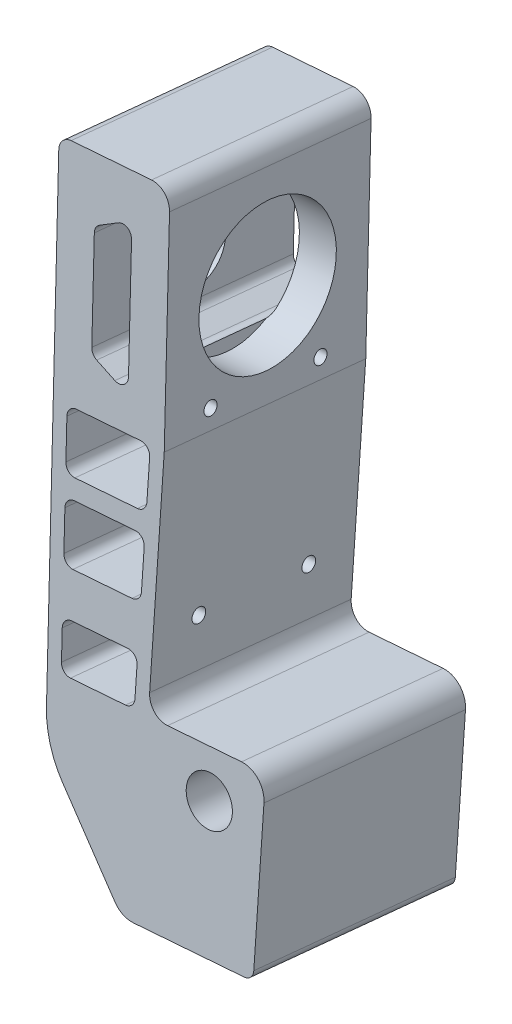
SolidWorks part; units mm, degrees
ref_plane "Front Plane" through (0, 0, 0) normal (0, 0, 1) x (1, 0, 0)
ref_plane "Top Plane" through (0, 0, 0) normal (0, 1, 0) x (1, 0, 0)
ref_plane "Right Plane" through (0, 0, 0) normal (1, 0, 0) x (0, 0, -1)
sketch "Sketch2" plane through (0, 5.1848, 52.754) normal (0, 0.0978, 0.9952) x (1, 0, 0)
  line L0 (-79.3386, 60.0196) -> (-86.1713, 157.1826)
  line L1 (-83.7601, 159.9586) -> (-66.4029, 161.1792)
  line L3 (-53.886, 68.8298) -> (-37.9279, 69.952)
  line L4 (-32.5786, 65.0833) -> (-31.8669, 35.1988)
  line L5 (-33.726, 33.1561) -> (-57.6669, 31.4725)
  line L6 (-61.8472, 33.2455) -> (-74.7061, 48.5637)
  line L9 (-57.6669, 31.4725) -> (-58.0176, 36.4602) construction
  line L11 (-69.4667, 77.7588) -> (-69.797, 86.7578) construction
  line L13 (-62.1322, 157.4697) -> (-59.1859, 115.5731)
  line L14 (-59.1859, 115.5731) -> (-58.1655, 72.7247)
  line L18 (-62.9661, 68.1912) -> (-74.8421, 67.3561)
  line L19 (-76.9775, 69.2109) -> (-77.3984, 75.1961)
  line L21 (-63.8004, 103.219) -> (-77.2973, 102.2699)
  line L23 (-79.4327, 104.1246) -> (-79.9939, 112.1049)
  line L24 (-62.1319, 113.268) -> (-61.9412, 105.2617)
  line L28 (-76.6898, 136.3966) -> (-77.3913, 146.3719)
  line L29 (-63.419, 87.2063) -> (-76.175, 86.3093)
  line L30 (-59.1859, 115.5731) -> (-83.1268, 113.8896) construction
  line L31 (-76.4139, 148.2339) -> (-72.5641, 150.5096)
  line L32 (-78.1391, 114.2403) -> (-64.2716, 115.2155)
  line L33 (-69.5513, 148.9282) -> (-68.7095, 136.9577)
  line L35 (-78.3103, 88.1641) -> (-78.8715, 96.1443)
  line L36 (-76.6898, 136.3966) -> (-68.7095, 136.9577) construction
  line L37 (-76.6898, 136.3966) -> (-68.7095, 136.9577) construction
  line L38 (-67.8677, 124.9873) -> (-68.7095, 136.9577)
  line L39 (-74.76, 124.7143) -> (-70.6295, 122.9998)
  line L40 (-76.6898, 136.3966) -> (-75.9883, 126.4212)
  line L41 (-61.7505, 97.2553) -> (-61.5599, 89.249)
  line L42 (-77.0168, 98.2797) -> (-63.8903, 99.2028)
  line L43 (-61.25, 76.2387) -> (-61.107, 70.2339)
  line L44 (-75.5436, 77.3315) -> (-63.3897, 78.1861)
  arc A0 (-86.1713, 157.1826) -> (-83.7601, 159.9586) centre (-83.5777, 157.365) cw
  arc A1 (-66.4029, 161.1792) -> (-62.1322, 157.4697) centre (-66.1223, 157.1891) cw
  arc A2 (-58.1655, 72.7247) -> (-53.886, 68.8298) centre (-54.1666, 72.8199) ccw
  arc A3 (-37.9279, 69.952) -> (-32.5786, 65.0833) centre (-37.5772, 64.9643) cw
  arc A4 (-31.8669, 35.1988) -> (-33.726, 33.1561) centre (-33.8663, 35.1512) cw
  arc A6 (-74.7061, 48.5637) -> (-79.3386, 60.0196) centre (-59.3878, 61.4226) cw
  circle A7 centre (-43.9609, 60.0043) radius 5
  arc A16 (-77.2973, 102.2699) -> (-79.4327, 104.1246) centre (-77.4376, 104.2649) cw
  arc A17 (-79.9939, 112.1049) -> (-78.1391, 114.2403) centre (-77.9988, 112.2452) cw
  arc A21 (-72.5641, 150.5096) -> (-69.5513, 148.9282) centre (-71.5464, 148.7879) cw
  arc A24 (-77.3913, 146.3719) -> (-76.4139, 148.2339) centre (-75.3962, 146.5122) cw
  arc A26 (-70.6295, 122.9998) -> (-67.8677, 124.9873) centre (-69.8628, 124.847) ccw
  arc A27 (-75.9883, 126.4212) -> (-74.76, 124.7143) centre (-73.9932, 126.5615) ccw
  arc A28 (-64.2716, 115.2155) -> (-62.1319, 113.268) centre (-64.1313, 113.2204) cw
  arc A29 (-61.9412, 105.2617) -> (-63.8004, 103.219) centre (-63.9407, 105.2141) cw
  arc A30 (-76.175, 86.3093) -> (-78.3103, 88.1641) centre (-76.3153, 88.3044) cw
  arc A31 (-78.8715, 96.1443) -> (-77.0168, 98.2797) centre (-76.8765, 96.2846) cw
  arc A32 (-63.8903, 99.2028) -> (-61.7505, 97.2553) centre (-63.75, 97.2077) cw
  arc A33 (-61.5599, 89.249) -> (-63.419, 87.2063) centre (-63.5593, 89.2014) cw
  arc A34 (-74.8421, 67.3561) -> (-76.9775, 69.2109) centre (-74.9824, 69.3512) cw
  arc A35 (-77.3984, 75.1961) -> (-75.5436, 77.3315) centre (-75.4033, 75.3364) cw
  arc A36 (-63.3897, 78.1861) -> (-61.25, 76.2387) centre (-63.2494, 76.1911) cw
  arc A37 (-61.107, 70.2339) -> (-62.9661, 68.1912) centre (-63.1064, 70.1863) cw
  arc A38 (-61.8472, 33.2455) -> (-57.6669, 31.4725) centre (-58.0176, 36.4602) ccw
  point P19 (-71.1564, 114.7313)
  point P44 (-57.6669, 82.2583)
  point P62 (-59.1859, 115.5731)
  point P109 (-69.1304, 142.943)
  point P116 (-77.0405, 141.3842)
  point P123 (-72.6997, 136.6771)
  dimension "D3" = 4
  dimension "D6" = 5
  dimension "D9" = 2
  dimension "D10" = 20
  dimension "D12" = 2
  dimension "D11" = 2
  dimension "D23" = 2
  dimension "D24" = 2
  dimension "D25" = 2
  dimension "D26" = 2
  dimension "D29" = 2
  dimension "D30" = 2
  dimension "D31" = 2
  dimension "D32" = 2
  dimension "D38" = 2
  dimension "D39" = 2
  dimension "D40" = 2
  dimension "D41" = 2
  dimension "D44" = 10
  dimension "D8" = 5
  dimension "D18" = 24
  dimension "D19" = 24
  dimension "D13" = 8
  dimension "D14" = 8
  dimension "D15" = 8
  dimension "D16" = 10
  dimension "D17" = 12
  dimension "D20" = 3
  dimension "D22" = 3
  dimension "D27" = 12
  dimension "D28" = 3
  dimension "D33" = 3
  dimension "D34" = 4
  dimension "D35" = 12
  dimension "D36" = 9
  dimension "D21" = 46
  dimension "D37" = 10
  dimension "D42" = 3
  dimension "D43" = 3
  dimension "D5" = 37
  dimension "D7" = 47
  dimension "D45" = 24
  dimension "D46" = 20
  dimension "D47" = 11.5
  dimension "D48" = 9.5
extrude "Boss-Extrude1" add sketch "Sketch2" along normal blind 44
sketch "Sketch3" plane through (-50.8073, -3.5558, 0.3495) normal (0.9975, 0.0698, -0.0069) x (-0.0068, -0.0005, -1)
  line L0 (-80.7931, 170.1353) -> (-37.0031, 165.8421) construction
  line L1 (-84.8912, 128.3357) -> (-80.7931, 170.1353) construction
  line L2 (-82.8422, 149.2355) -> (-39.0521, 144.9423) construction
  line L3 (-41.1011, 124.0425) -> (-37.0031, 165.8421) construction
  line L4 (-58.8981, 167.9887) -> (-62.9962, 126.1891) construction
  line L5 (-84.8912, 128.3357) -> (-41.1011, 124.0425) construction
  line L6 (-74.5486, 131.3409) -> (-79.1164, 84.7498) construction
  line L7 (-89.0687, 85.7255) -> (-84.8912, 128.3357) construction
  line L8 (-89.0687, 85.7255) -> (-45.2787, 81.4323) construction
  circle A0 centre (-60.9471, 147.0889) radius 15
  circle A1 centre (-74.5486, 131.3409) radius 1.4323
  circle A2 centre (-78.1407, 94.7021) radius 1.5
  circle A3 centre (-54.2552, 92.3603) radius 1.5
  circle A4 centre (-50.6631, 128.9991) radius 1.4323
  point P0 (-58.8981, 167.9887)
  point P1 (-82.8422, 149.2355)
  point P20 (-80.2119, 94.0736)
  dimension "D1" = 30
  dimension "D4" = 2.8645
  dimension "D5" = 3
  dimension "D2" = 4
  dimension "D3" = 10
  dimension "D6" = 10
sketch "Sketch4" plane through (-74.7482, -5.2313, 0.5141) normal (-0.9975, -0.0698, 0.0069) x (0.0068, 0.0005, 1)
  circle A0 centre (60.9471, 147.0889) radius 7
  dimension "D1" = 14
extrude "Cut-Extrude1" cut sketch "Sketch4" against normal blind 44
extrude "Cut-Extrude2" cut sketch "Sketch3" against normal blind 8.5
equation "\"radius2mm\"=2"
equation "\"distance3mm\"=3"
equation "\"D20@Sketch2\"=\"distance3mm\""
equation "\"D22@Sketch2\"=\"distance3mm\""
equation "\"D28@Sketch2\"=\"distance3mm\""
equation "\"D9@Sketch2\"=\"radius2mm\""
